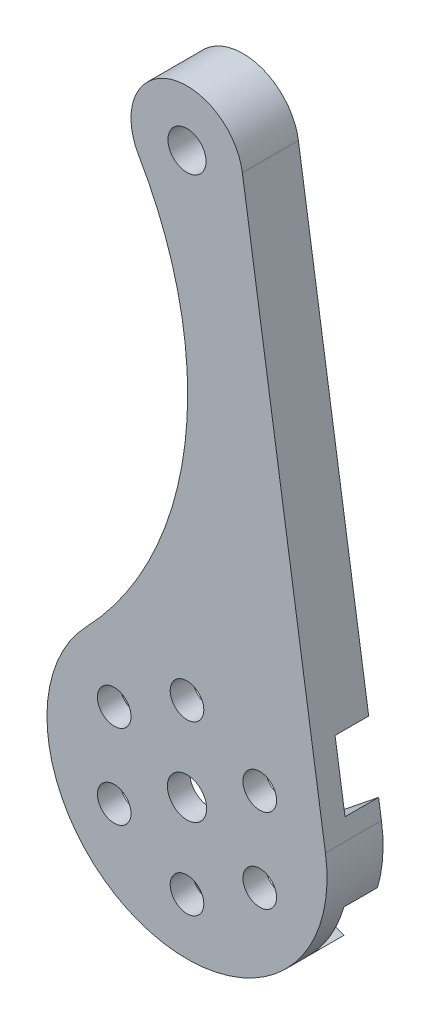
SolidWorks part; units mm, degrees
ref_plane "前视基准面" through (0, 0, 0) normal (0, 0, 1) x (1, 0, 0)
ref_plane "上视基准面" through (0, 0, 0) normal (0, 1, 0) x (1, 0, 0)
ref_plane "右视基准面" through (0, 0, 0) normal (1, 0, 0) x (0, 0, -1)
sketch "草图1" plane through (0, 0, 0) normal (0, 0, 1) x (1, 0, 0)
  line L0 (0, 0) -> (0, 50) construction
  line L1 (4.9434, 50.75) -> (12.3586, 1.875)
  arc A0 (-9.0106, 8.6637) -> (12.3586, 1.875) centre (0, 0) ccw
  arc A1 (4.9434, 50.75) -> (-4.3251, 47.4914) centre (0, 50) ccw
  arc A2 (-4.3251, 47.4914) -> (-9.0106, 8.6637) centre (-32.4358, 31.187) cw
  circle A3 centre (0, 50) radius 1.7
  circle A4 centre (0, 0) radius 1.75
  circle A5 centre (-6.4952, -3.75) radius 1.5
  circle A6 centre (-6.4952, 3.75) radius 1.5
  circle A7 centre (0, 7.5) radius 1.5
  circle A8 centre (6.4952, 3.75) radius 1.5
  circle A9 centre (6.4952, -3.75) radius 1.5
  circle A10 centre (0, -7.5) radius 1.5
  point P25 (0, 0)
  dimension "D1" = 10
  dimension "D2" = 25
  dimension "D4" = 6
  dimension "D3" = 50
extrude "凸台-拉伸1" add sketch "草图1" along normal blind 2
sketch "草图2" plane through (0, 0, 0) normal (0, 0, -1) x (-1, 0, 0)
  line L0 (-12.1046, 3.549) -> (-12.3586, 1.875)
  line L1 (-4.9434, 50.75) -> (-12.3586, 1.875)
  line L2 (-4.9434, 50.75) -> (-11.2181, 9.3919)
  line L26 (10.4181, 9.2102) -> (3.8438, 6.6576)
  line L27 (7.6876, 0) -> (13.1853, 4.4173)
  line L28 (13.1853, -4.4173) -> (7.6876, 0)
  line L29 (3.8438, -6.6576) -> (10.4181, -9.2102)
  line L30 (2.7672, -13.6274) -> (3.8438, -6.6576)
  line L31 (-3.8438, -6.6576) -> (-2.7672, -13.6274)
  line L32 (-10.4181, -9.2102) -> (-3.8438, -6.6576)
  line L33 (-7.6876, 0) -> (-13.1853, -4.4173)
  line L34 (-13.1853, 4.4173) -> (-7.6876, 0)
  line L35 (-3.8438, 6.6576) -> (-10.4181, 9.2102)
  line L36 (-2.7672, 13.6274) -> (-3.8438, 6.6576)
  line L37 (3.8438, 6.6576) -> (2.7672, 13.6274)
  line L38 (9.0106, 8.6637) -> (3.8438, 6.6576)
  line L39 (7.6876, 0) -> (12.0083, 3.4716)
  line L40 (12.0083, -3.4716) -> (7.6876, 0)
  line L41 (3.8438, -6.6576) -> (9.0106, -8.6637)
  line L42 (2.9977, -12.1352) -> (3.8438, -6.6576)
  line L43 (-3.8438, -6.6576) -> (-2.9977, -12.1352)
  line L44 (-9.0106, -8.6637) -> (-3.8438, -6.6576)
  line L45 (-7.6876, 0) -> (-12.0083, -3.4716)
  line L46 (-12.1046, 3.549) -> (-7.6876, 0)
  line L47 (-3.8438, 6.6576) -> (-10.4181, 9.2102)
  line L48 (-2.7672, 13.6274) -> (-3.8438, 6.6576)
  line L49 (3.8438, 6.6576) -> (2.7672, 13.6274)
  arc A0 (-9.0106, -8.6637) -> (-2.9977, -12.1352) centre (0, 0) ccw
  arc A1 (2.9977, -12.1352) -> (9.0106, -8.6637) centre (0, 0) ccw
  arc A2 (12.0083, -3.4716) -> (12.0083, 3.4716) centre (0, 0) ccw
  arc A3 (4.3251, 47.4914) -> (-4.9434, 50.75) centre (0, 50) ccw
  arc A4 (-12.3586, 1.875) -> (9.0106, 8.6637) centre (0, 0) ccw
  arc A5 (4.3251, 47.4914) -> (9.0106, 8.6637) centre (32.4358, 31.187) ccw
  arc A6 (4.3251, 47.4914) -> (-4.9434, 50.75) centre (0, 50) ccw
  arc A7 (-12.3586, 1.875) -> (-12.0083, -3.4716) centre (0, 0) ccw
  arc A8 (4.3251, 47.4914) -> (9.0106, 8.6637) centre (32.4358, 31.187) ccw
  circle A9 centre (0, 50) radius 1.7 construction
  circle A10 centre (0, 50) radius 1.7
  arc A18 (13.1853, 4.4173) -> (10.4181, 9.2102) centre (11.4315, 6.6) ccw
  arc A19 (10.4181, -9.2102) -> (13.1853, -4.4173) centre (11.4315, -6.6) ccw
  arc A20 (-2.7672, -13.6274) -> (2.7672, -13.6274) centre (0, -13.2) ccw
  arc A21 (-13.1853, -4.4173) -> (-10.4181, -9.2102) centre (-11.4315, -6.6) ccw
  arc A22 (-10.4181, 9.2102) -> (-13.1853, 4.4173) centre (-11.4315, 6.6) ccw
  arc A23 (2.7672, 13.6274) -> (-2.7672, 13.6274) centre (0, 13.2) ccw
  arc A28 (-10.4181, 9.2102) -> (-11.2181, 9.3919) centre (-11.4315, 6.6) ccw
  arc A29 (2.7672, 13.6274) -> (-2.7672, 13.6274) centre (0, 13.2) ccw
  dimension "D1" = 0
  dimension "D2" = 0.3
extrude "凸台-拉伸2" add sketch "草图2" along normal blind 3
